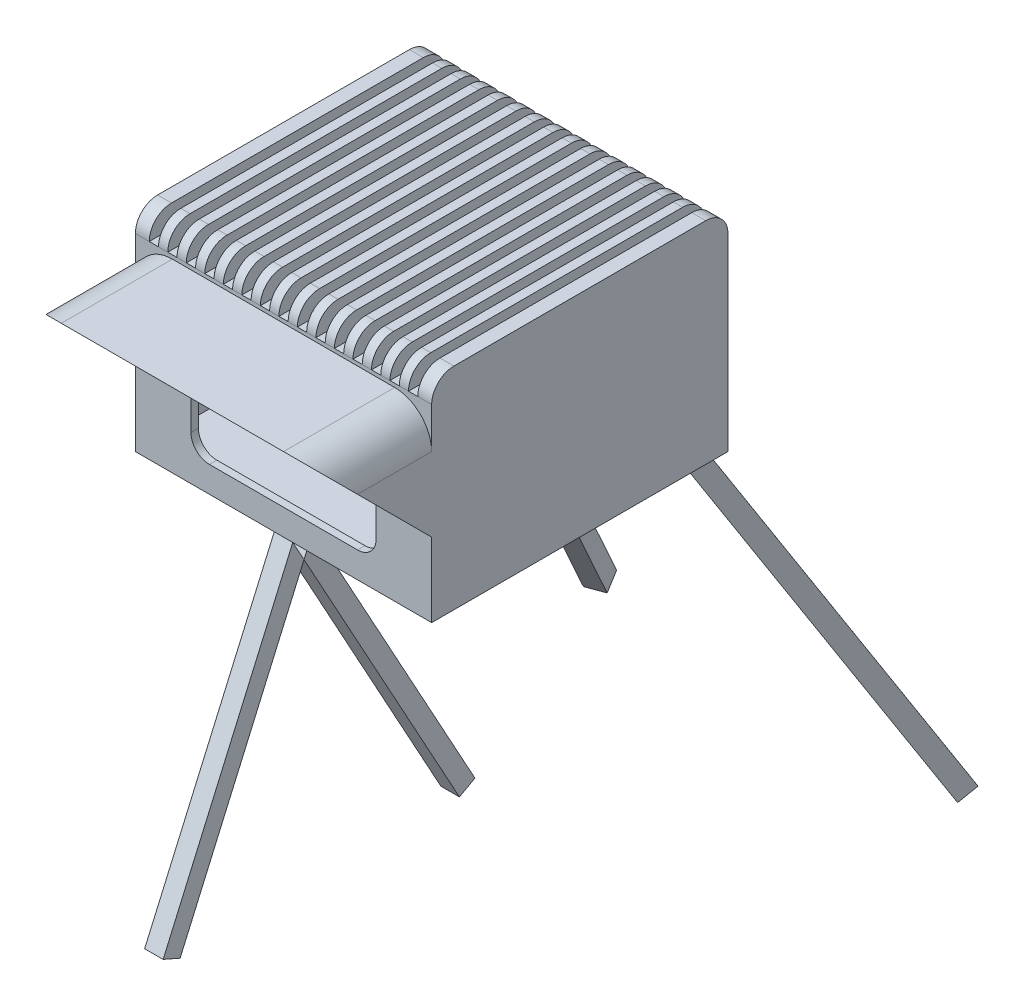
SolidWorks part; units mm, degrees
ref_plane "Front Plane" through (0, 0, 0) normal (0, 0, 1) x (1, 0, 0)
ref_plane "Top Plane" through (0, 0, 0) normal (0, 1, 0) x (1, 0, 0)
ref_plane "Right Plane" through (0, 0, 0) normal (1, 0, 0) x (0, 0, -1)
sketch "Sketch1" plane through (0, 0, 0) normal (0, 1, 0) x (1, 0, 0)
  line L1 (-50.8, -50.8) -> (50.8, -50.8)
  line L2 (-50.8, -50.8) -> (-50.8, 50.8)
  line L3 (-50.8, 50.8) -> (50.8, 50.8)
  line L4 (50.8, -50.8) -> (50.8, 50.8)
  point P4 (50.8, 0)
  point P6 (0, 50.8)
  dimension "D1" = 101.6
  dimension "D2" = 101.6
extrude "Boss-Extrude1" add sketch "Sketch1" along normal blind 63.5
shell "Shell1" thickness 2.54
sketch "Sketch3" plane through (0, 0, 50.8) normal (0, 0, 1) x (1, 0, 0)
  line L0 (0, -34.925) -> (0, 34.925) construction
  line L1 (-25.4, 46.99) -> (25.4, 46.99)
  line L2 (-31.75, 40.64) -> (-31.75, 15.24)
  line L3 (-25.4, 8.89) -> (25.4, 8.89)
  line L4 (31.75, 40.64) -> (31.75, 15.24)
  line L5 (55.88, 0) -> (-55.88, 0) construction
  arc A0 (31.75, 40.64) -> (25.4, 46.99) centre (25.4, 40.64) ccw
  arc A1 (31.75, 15.24) -> (25.4, 8.89) centre (25.4, 15.24) cw
  arc A2 (-25.4, 8.89) -> (-31.75, 15.24) centre (-25.4, 15.24) cw
  arc A3 (-31.75, 40.64) -> (-25.4, 46.99) centre (-25.4, 40.64) cw
  point P4 (0, 46.99)
  dimension "D1" = 6.35
  dimension "D2" = 38.1
  dimension "D3" = 63.5
  dimension "D4" = 8.89
extrude "Cut-Extrude2" cut sketch "Sketch3" against normal up to next
sketch "Sketch4" plane through (0, 2.54, 0) normal (0, 1, 0) x (1, 0, 0)
  line L0 (0, -34.925) -> (0, 34.925) construction
  line L1 (-38.1, -25.4) -> (38.1, -25.4)
  line L2 (-38.1, -25.4) -> (-38.1, -22.225)
  line L3 (-38.1, -22.225) -> (38.1, -22.225)
  line L4 (38.1, -25.4) -> (38.1, -22.225)
  line L5 (-50.8, -50.8) -> (50.8, -50.8) construction
  point P4 (0, -25.4)
  dimension "D1" = 76.2
  dimension "D2" = 3.175
  dimension "D3" = 25.4
extrude "Boss-Extrude2" add sketch "Sketch4" along normal blind 50.8
sketch "Sketch5" plane through (0, 0, 25.4) normal (0, 0, 1) x (1, 0, 0)
  line L0 (0, 34.4156) -> (0, 0) construction
  line L1 (-38.1, 2.54) -> (38.1, 2.54) construction
  circle A0 centre (-25.4, 43.18) radius 1.5875
  circle A1 centre (25.4, 43.18) radius 1.5875
  dimension "D2" = 3.175
  dimension "D1" = 25.4
  dimension "D3" = 40.64
extrude "Cut-Extrude3" cut sketch "Sketch5" against normal up to next
sketch "Sketch6" plane through (0, 63.5, 0) normal (0, 1, 0) x (1, 0, 0)
  line L0 (-48.26, 48.26) -> (-48.26, -48.26) construction
  line L1 (-48.26, -48.26) -> (48.26, -48.26) construction
  line L2 (48.26, -48.26) -> (48.26, 48.26) construction
  line L3 (48.26, 48.26) -> (-48.26, 48.26) construction
  line L4 (-48.26, -39.37) -> (-48.26, -48.26)
  line L5 (-48.26, -48.26) -> (-39.37, -48.26)
  line L6 (39.37, -48.26) -> (48.26, -48.26)
  line L7 (48.26, -48.26) -> (48.26, -39.37)
  line L8 (48.26, 39.37) -> (48.26, 48.26)
  line L9 (48.26, 48.26) -> (39.37, 48.26)
  line L10 (-48.26, 39.37) -> (-48.26, 48.26)
  line L11 (-48.26, 48.26) -> (-39.37, 48.26)
  arc A0 (-48.26, -39.37) -> (-39.37, -48.26) centre (-48.26, -48.26) cw
  arc A1 (39.37, -48.26) -> (48.26, -39.37) centre (48.26, -48.26) cw
  arc A2 (48.26, 39.37) -> (39.37, 48.26) centre (48.26, 48.26) cw
  arc A3 (-48.26, 39.37) -> (-39.37, 48.26) centre (-48.26, 48.26) ccw
  dimension "D1" = 8.89
extrude "Boss-Extrude3" add sketch "Sketch6" against normal blind 19.05
sketch "Sketch7" plane through (0, 0, 50.8) normal (0, 0, 1) x (1, 0, 0)
  line L0 (-50.8, 14.6825) -> (-47.8312, 14.6825)
  line L1 (-50.8, 63.5) -> (-50.8, 0) construction
  line L2 (38.1, 63.5) -> (-38.1, 63.5)
  line L3 (-50.8, 63.5) -> (50.8, 63.5) construction
  line L4 (-50.8, 50.8) -> (-50.8, 25.4)
  line L5 (-50.8, 25.4) -> (-49.2125, 25.4)
  line L6 (-49.2125, 25.4) -> (-49.2125, 50.8)
  line L7 (-38.1, 61.9125) -> (38.1, 61.9125)
  line L9 (0, 63.5) -> (0, 61.9125) construction
  line L10 (49.2125, 25.4) -> (49.2125, 50.8)
  line L11 (50.8, 25.4) -> (49.2125, 25.4)
  line L12 (50.8, 50.8) -> (50.8, 25.4)
  arc A0 (-38.1, 63.5) -> (-50.8, 50.8) centre (-38.1, 50.8) ccw
  arc A1 (-38.1, 61.9125) -> (-49.2125, 50.8) centre (-38.1, 50.8) ccw
  arc A2 (38.1, 61.9125) -> (49.2125, 50.8) centre (38.1, 50.8) cw
  arc A3 (38.1, 63.5) -> (50.8, 50.8) centre (38.1, 50.8) cw
  line M19 (50.8, 0) -> (50.8, 63.5)
  line M20 (50.8, 63.5) -> (-50.8, 63.5)
  line M21 (-50.8, 63.5) -> (-50.8, 0)
  dimension "D2" = 12.7
  dimension "D1" = 1.5875
  dimension "D3" = 38.1
extrude "Boss-Extrude4" add sketch "Sketch7" along normal blind 38.1 contours L9 L2 A0 L5 L6 A1 L7 M21 | L9 L7 A2 L10 L11 A3 M20 M19
sketch "Sketch8" plane through (-50.8, 0, 0) normal (-1, 0, 0) x (0, 0, 1)
  line L0 (50.8, 25.4) -> (88.9, 63.5)
  line L1 (50.8, 25.4) -> (50.8, 0) construction
  line L2 (88.9, 25.4) -> (50.8, 25.4) construction
  line L7 (88.9, 25.4) -> (88.9, 63.5) construction
  line L8 (50.8, 25.4) -> (88.9, 25.4)
  line L9 (88.9, 25.4) -> (88.9, 63.5)
  line L10 (50.8, 63.5) -> (88.9, 63.5) construction
extrude "Cut-Extrude4" cut sketch "Sketch8" against normal through all
sketch "Sketch9" plane through (0, 0, 0) normal (1, 0, 0) x (0, 0, -1)
  line L0 (-50.8, 0) -> (-95.25, -101.6)
  line L1 (-95.25, -101.6) -> (-89.4324, -104.1452)
  line L2 (-89.4324, -104.1452) -> (-43.8689, 0)
  line L3 (-43.8689, 0) -> (-50.8, 0)
  line L4 (-50.8, 25.4) -> (-50.8, 0) construction
  line L5 (50.8, 0) -> (-50.8, 0) construction
  line L6 (-50.8, 0) -> (6.35, -104.1452)
  line L7 (6.35, -104.1452) -> (11.677, -101.222)
  line L8 (11.677, -101.222) -> (-43.8689, 0)
  point P6 (0, 0)
  dimension "D1" = 44.45
  dimension "D2" = 6.35
  dimension "D3" = 101.6
  dimension "D4" = 101.6
extrude "Boss-Extrude5" add sketch "Sketch9" along normal mid plane 6.35 contours L7 L8 L2 L6 | L6 L0 L1 L2
sketch "Sketch10" plane through (0, 0, 0) normal (0, -1, 0) x (1, 0, 0)
  line L0 (0, 50.8) -> (0, -50.8) construction
  line L2 (50.8, -50.8) -> (-50.8, -50.8) construction
  line L3 (0, 50.8) -> (36.9794, -50.8) construction
  line L4 (0, 50.8) -> (-36.9794, -50.8) construction
  line L5 (3.175, 50.8) -> (-3.175, 50.8) construction
  point P2 (0, 48.5093)
  point P8 (0, 0)
  point P10 (0, 50.8)
  dimension "D1" = 20
ref_plane "Plane1" through (16.3268, 0, 5.9425) normal (0.9397, 0, 0.342) x (0.342, 0, -0.9397)
sketch "Sketch11" plane through (16.3268, 0, 5.9425) normal (0.9397, 0, 0.342) x (0.342, 0, -0.9397)
  line L0 (60.3841, 0) -> (136.5841, -127)
  line L1 (136.5841, -127) -> (131.139, -130.267)
  line L2 (131.139, -130.267) -> (52.9788, 0)
  line L3 (52.9788, 0) -> (60.3841, 0)
  dimension "D1" = 6.35
  dimension "D2" = 127
  dimension "D3" = 76.2
extrude "Boss-Extrude6" add sketch "Sketch11" along normal mid plane 6.35
mirror "Mirror1" about plane through (0, 0, 0) normal (1, 0, 0) of "Boss-Extrude6"
sketch "Sketch12" plane through (0, 63.5, 0) normal (0, 1, 0) x (1, 0, 0)
  line L1 (-50.8, -50.8) -> (50.8, -50.8)
  line L2 (-50.8, -50.8) -> (-50.8, 50.8)
  line L3 (-50.8, 50.8) -> (50.8, 50.8)
  line L4 (50.8, -50.8) -> (50.8, 50.8)
extrude "Boss-Extrude7" add sketch "Sketch12" along normal blind 8.89
sketch "Sketch13" plane through (0, 72.39, 0) normal (0, 1, 0) x (1, 0, 0)
  line L0 (50.8, 50.8) -> (-50.8, 50.8) construction
  line L1 (-1.5875, 50.8) -> (1.5875, 50.8)
  line L2 (-1.5875, 50.8) -> (-1.5875, -50.8)
  line L3 (-1.5875, -50.8) -> (1.5875, -50.8)
  line L4 (1.5875, 50.8) -> (1.5875, -50.8)
  line L5 (-50.8, -50.8) -> (50.8, -50.8) construction
  line L6 (-7.9375, 50.8) -> (-7.9375, -50.8)
  line L7 (-7.9375, -50.8) -> (-4.7625, -50.8)
  line L8 (-4.7625, 50.8) -> (-4.7625, -50.8)
  line L9 (-7.9375, 50.8) -> (-4.7625, 50.8)
  line L10 (-14.2875, 50.8) -> (-14.2875, -50.8)
  line L11 (-14.2875, -50.8) -> (-11.1125, -50.8)
  line L12 (-11.1125, 50.8) -> (-11.1125, -50.8)
  line L13 (-14.2875, 50.8) -> (-11.1125, 50.8)
  line L14 (-20.6375, 50.8) -> (-20.6375, -50.8)
  line L15 (-20.6375, -50.8) -> (-17.4625, -50.8)
  line L16 (-17.4625, 50.8) -> (-17.4625, -50.8)
  line L17 (-20.6375, 50.8) -> (-17.4625, 50.8)
  line L18 (-26.9875, 50.8) -> (-26.9875, -50.8)
  line L19 (-26.9875, -50.8) -> (-23.8125, -50.8)
  line L20 (-23.8125, 50.8) -> (-23.8125, -50.8)
  line L21 (-26.9875, 50.8) -> (-23.8125, 50.8)
  line L22 (-33.3375, 50.8) -> (-33.3375, -50.8)
  line L23 (-33.3375, -50.8) -> (-30.1625, -50.8)
  line L24 (-30.1625, 50.8) -> (-30.1625, -50.8)
  line L25 (-33.3375, 50.8) -> (-30.1625, 50.8)
  line L26 (-39.6875, 50.8) -> (-39.6875, -50.8)
  line L27 (-39.6875, -50.8) -> (-36.5125, -50.8)
  line L28 (-36.5125, 50.8) -> (-36.5125, -50.8)
  line L29 (-39.6875, 50.8) -> (-36.5125, 50.8)
  line L30 (-46.0375, 50.8) -> (-46.0375, -50.8)
  line L31 (-46.0375, -50.8) -> (-42.8625, -50.8)
  line L32 (-42.8625, 50.8) -> (-42.8625, -50.8)
  line L33 (-46.0375, 50.8) -> (-42.8625, 50.8)
  line L34 (4.7625, 50.8) -> (4.7625, -50.8)
  line L35 (4.7625, -50.8) -> (7.9375, -50.8)
  line L36 (7.9375, 50.8) -> (7.9375, -50.8)
  line L37 (4.7625, 50.8) -> (7.9375, 50.8)
  line L38 (11.1125, 50.8) -> (11.1125, -50.8)
  line L39 (11.1125, -50.8) -> (14.2875, -50.8)
  line L40 (14.2875, 50.8) -> (14.2875, -50.8)
  line L41 (11.1125, 50.8) -> (14.2875, 50.8)
  line L42 (17.4625, 50.8) -> (17.4625, -50.8)
  line L43 (17.4625, -50.8) -> (20.6375, -50.8)
  line L44 (20.6375, 50.8) -> (20.6375, -50.8)
  line L45 (17.4625, 50.8) -> (20.6375, 50.8)
  line L46 (23.8125, 50.8) -> (23.8125, -50.8)
  line L47 (23.8125, -50.8) -> (26.9875, -50.8)
  line L48 (26.9875, 50.8) -> (26.9875, -50.8)
  line L49 (23.8125, 50.8) -> (26.9875, 50.8)
  line L50 (30.1625, 50.8) -> (30.1625, -50.8)
  line L51 (30.1625, -50.8) -> (33.3375, -50.8)
  line L52 (33.3375, 50.8) -> (33.3375, -50.8)
  line L53 (30.1625, 50.8) -> (33.3375, 50.8)
  line L54 (36.5125, 50.8) -> (36.5125, -50.8)
  line L55 (36.5125, -50.8) -> (39.6875, -50.8)
  line L56 (39.6875, 50.8) -> (39.6875, -50.8)
  line L57 (36.5125, 50.8) -> (39.6875, 50.8)
  line L58 (42.8625, 50.8) -> (42.8625, -50.8)
  line L59 (42.8625, -50.8) -> (46.0375, -50.8)
  line L60 (46.0375, 50.8) -> (46.0375, -50.8)
  line L61 (42.8625, 50.8) -> (46.0375, 50.8)
  point P8 (0, 50.8)
  point P9 (0, 50.8)
  dimension "D1" = 3.175
  dimension "D2" = 8
  dimension "D3" = 8
extrude "Cut-Extrude5" cut sketch "Sketch13" against normal blind 7.62
fillet "Fillet1" radius 7.62 32 edges at (48.4187, 72.39, -50.8) (41.275, 72.39, -50.8) (34.925, 72.39, -50.8) (28.575, 72.39, -50.8) (22.225, 72.39, -50.8) (15.875, 72.39, -50.8) (9.525, 72.39, -50.8) (3.175, 72.39, -50.8) (-3.175, 72.39, -50.8) (-9.525, 72.39, -50.8) (-15.875, 72.39, -50.8) (-22.225, 72.39, -50.8) (-28.575, 72.39, -50.8) (-34.925, 72.39, -50.8) (-41.275, 72.39, -50.8) (-48.4187, 72.39, -50.8) (48.4187, 72.39, 50.8) (41.275, 72.39, 50.8) (34.925, 72.39, 50.8) (28.575, 72.39, 50.8) (22.225, 72.39, 50.8) (15.875, 72.39, 50.8) (9.525, 72.39, 50.8) (3.175, 72.39, 50.8) (-3.175, 72.39, 50.8) (-9.525, 72.39, 50.8) (-15.875, 72.39, 50.8) (-22.225, 72.39, 50.8) (-28.575, 72.39, 50.8) (-34.925, 72.39, 50.8) (-41.275, 72.39, 50.8) (-48.4187, 72.39, 50.8)
